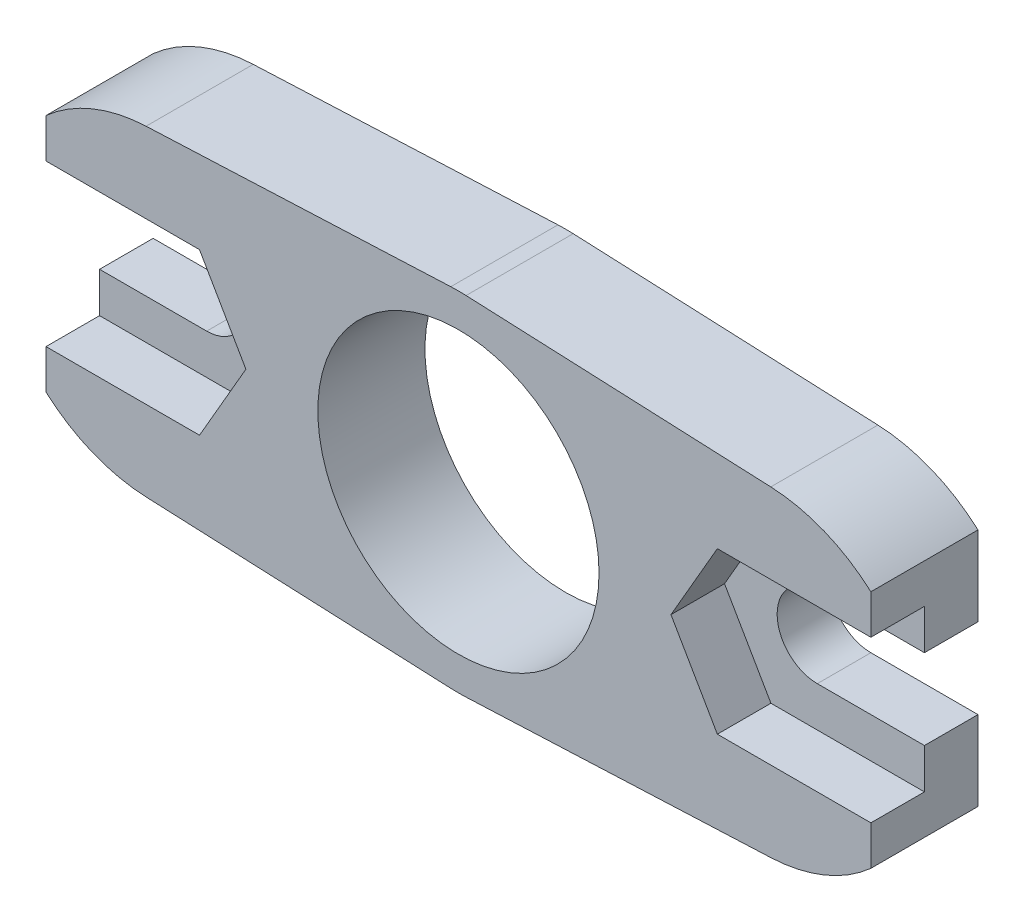
SolidWorks part; units mm, degrees
material "ABS"
ref_plane "Спереди" through (0, 0, 0) normal (0, 0, 1) x (1, 0, 0)
ref_plane "Сверху" through (0, 0, 0) normal (0, 1, 0) x (1, 0, 0)
ref_plane "Справа" through (0, 0, 0) normal (1, 0, 0) x (0, 0, -1)
sketch "Эскиз1" plane through (0, 0, 0) normal (0, 0, 1) x (1, 0, 0)
  line L0 (-136.3368, -147.4942) -> (-147.7149, -147.9937)
  line L1 (-148.2851, -147.9937) -> (-159.6632, -147.4942)
  line L2 (-159.4, -140) -> (-163.4, -140)
  line L3 (-159.6632, -135.5058) -> (-148.2851, -135.0063)
  line L4 (-147.7149, -135.0063) -> (-136.3368, -135.5058)
  line L5 (-136.6, -140) -> (-132.6, -140)
  line L6 (-163.4, -143) -> (-159.4, -143)
  line L7 (-163.4, -137.0279) -> (-163.4, -140)
  line L8 (-136.6, -143) -> (-132.6, -143)
  line L9 (-163.4, -143) -> (-163.4, -145.9721)
  line L10 (-132.6, -145.9721) -> (-132.6, -143)
  line L11 (-132.6, -140) -> (-132.6, -137.0279)
  arc A0 (-148.2851, -147.9937) -> (-147.7149, -147.9937) centre (-148, -141.5) ccw
  arc A1 (-159.6632, -135.5058) -> (-163.4, -137.0279) centre (-159.4, -141.5) ccw
  arc A2 (-136.3368, -147.4942) -> (-132.6, -145.9721) centre (-136.6, -141.5) ccw
  arc A3 (-136.6, -140) -> (-136.6, -143) centre (-136.6, -141.5) ccw
  arc A4 (-159.4, -143) -> (-159.4, -140) centre (-159.4, -141.5) ccw
  arc A5 (-147.7149, -135.0063) -> (-148.2851, -135.0063) centre (-148, -141.5) ccw
  arc A6 (-163.4, -145.9721) -> (-159.6632, -147.4942) centre (-159.4, -141.5) ccw
  arc A7 (-132.6, -137.0279) -> (-136.3368, -135.5058) centre (-136.6, -141.5) ccw
  dimension "D1" = 3
  dimension "D2" = 13
  dimension "D3" = 12
  dimension "D4" = 4
  dimension "D5" = 4
extrude "Бобышка-Вытянуть1" add sketch "Эскиз1" along normal blind 6
sketch "Эскиз2" plane through (0, 0, 6) normal (0, 0, 1) x (1, 0, 0)
  line L0 (-148, -135) -> (-148, -148) construction
  arc A0 (-147.7149, -135.0063) -> (-148.2851, -135.0063) centre (-148, -141.5) ccw construction
  arc A1 (-148.2851, -147.9937) -> (-147.7149, -147.9937) centre (-148, -141.5) ccw construction
  circle A2 centre (-148, -141.5) radius 5.25
  dimension "D1" = 10.5
extrude "Вырез-Вытянуть1" cut sketch "Эскиз2" against normal blind 10
sketch "Эскиз3" plane through (0, 0, 6) normal (0, 0, 1) x (1, 0, 0)
  line L0 (-161.1321, -138.5) -> (-163.4, -138.5)
  line L1 (-157.6679, -138.5) -> (-161.1321, -138.5)
  line L2 (-161.1321, -138.5) -> (-162.8641, -141.5)
  line L3 (-162.8641, -141.5) -> (-161.1321, -144.5)
  line L4 (-161.1321, -144.5) -> (-157.6679, -144.5)
  line L5 (-157.6679, -144.5) -> (-155.9359, -141.5)
  line L6 (-155.9359, -141.5) -> (-157.6679, -138.5)
  line L7 (-134.8679, -138.5) -> (-138.3321, -138.5)
  line L8 (-138.3321, -138.5) -> (-140.0641, -141.5)
  line L9 (-140.0641, -141.5) -> (-138.3321, -144.5)
  line L10 (-138.3321, -144.5) -> (-134.8679, -144.5)
  line L11 (-134.8679, -144.5) -> (-133.1359, -141.5)
  line L12 (-133.1359, -141.5) -> (-134.8679, -138.5)
  line L13 (-163.4, -137.0279) -> (-163.4, -140) construction
  line L14 (-163.4, -138.5) -> (-163.4, -144.5)
  line L15 (-163.4, -143) -> (-163.4, -145.9721) construction
  line L16 (-163.4, -144.5) -> (-161.1321, -144.5)
  line L17 (-134.8679, -144.5) -> (-132.6, -144.5)
  line L18 (-132.6, -145.9721) -> (-132.6, -143) construction
  line L19 (-132.6, -144.5) -> (-132.6, -138.5)
  line L20 (-132.6, -140) -> (-132.6, -137.0279) construction
  line L21 (-132.6, -138.5) -> (-134.8679, -138.5)
  circle A0 centre (-159.4, -141.5) radius 3 construction
  circle A1 centre (-136.6, -141.5) radius 3 construction
  arc M2 (-159.4, -140) -> (-159.4, -143) centre (-159.4, -141.5) cw
  line M3 (-159.4, -143) -> (-163.4, -143)
  line M4 (-163.4, -143) -> (-163.4, -145.9721)
  line M10 (-132.6, -145.9721) -> (-132.6, -143)
  line M11 (-132.6, -143) -> (-136.6, -143)
  arc M12 (-136.6, -143) -> (-136.6, -140) centre (-136.6, -141.5) cw
  line M13 (-136.6, -140) -> (-132.6, -140)
  line M14 (-132.6, -140) -> (-132.6, -137.0279)
  line M20 (-163.4, -137.0279) -> (-163.4, -140)
  line M21 (-163.4, -140) -> (-159.4, -140)
  dimension "D1" = 6
extrude "Вырез-Вытянуть2" cut sketch "Эскиз3" against normal blind 2 contours L21 L12 M14 M13 | L12 L7 L8 L9 L10 L11 M13 M11 M12 | L11 L17 M10 M11 | L5 L6 L1 L2 L3 L4 M21 M2 M3 | L2 L0 M20 M21 | L16 L3 M4 M3
sketch "Эскиз4" plane through (-132.6, 0, 0) normal (1, 0, 0) x (0, 0, -1)
  line L1 (-2, -134.0063) -> (0, -134.0063)
  line L2 (-2, -134.0063) -> (-2, -148.9937)
  line L3 (-2, -148.9937) -> (0, -148.9937)
  line L4 (0, -134.0063) -> (0, -148.9937)
  line L5 (-4, -138.5) -> (-4, -141.5) construction
  line L6 (0, -143) -> (0, -145.9721) construction
  line L7 (-6, -135.0063) -> (0, -135.0063) construction
  line L8 (-6, -147.9937) -> (0, -147.9937) construction
  dimension "D1" = 2
  dimension "D2" = 1
  dimension "D3" = 1
extrude "Вырез-Вытянуть3" cut sketch "Эскиз4" against normal through all
